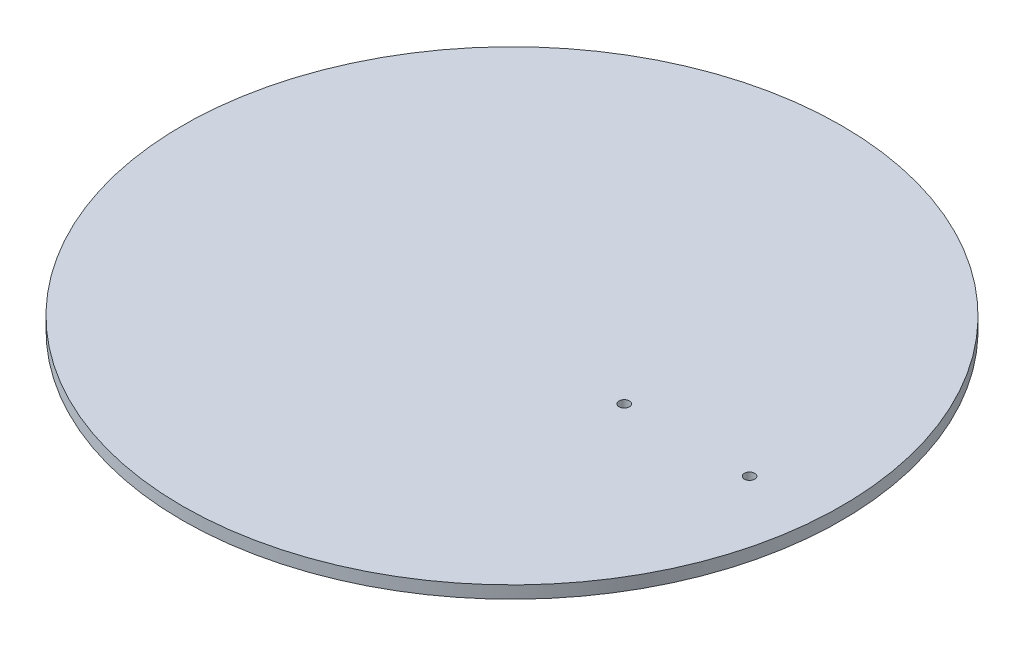
SolidWorks part; units mm, degrees
ref_plane "Front Plane" through (0, 0, 0) normal (0, 0, 1) x (1, 0, 0)
ref_plane "Top Plane" through (0, 0, 0) normal (0, 1, 0) x (1, 0, 0)
ref_plane "Right Plane" through (0, 0, 0) normal (1, 0, 0) x (0, 0, -1)
sketch "Record" plane through (0, 0, 0) normal (0, 1, 0) x (1, 0, 0)
  circle A0 centre (13.7433, -70.8416) radius 157.1625 construction
  circle A1 centre (13.7433, -70.8416) radius 39.7828 construction
  circle A4 centre (66.3721, -74.952) radius 1.0543
  circle A5 centre (40.7796, -74.952) radius 1.0543
  circle A14 centre (13.7433, -70.8416) radius 67.31
  point P4 (0, 0)
  point P9 (0, 0)
  dimension "D1" = 314.325
  dimension "D2" = 314.325
extrude "Record Extrude" add sketch "Record" along normal blind 2.54
